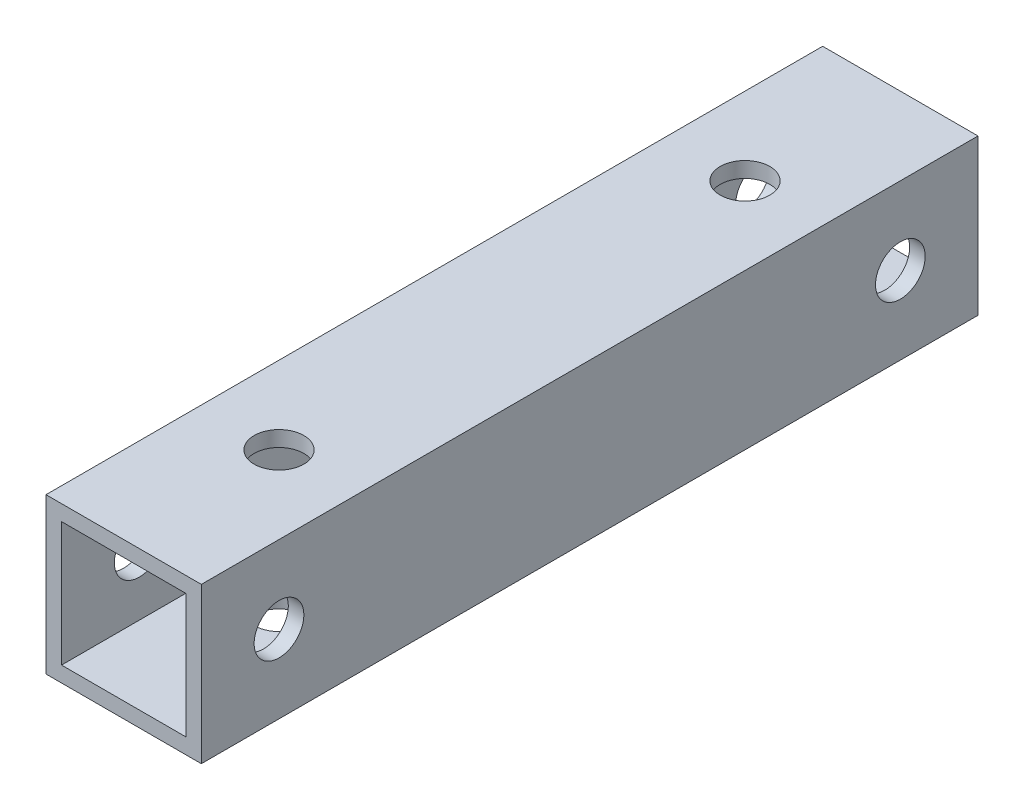
SolidWorks part; units mm, degrees
ref_plane "正面" through (0, 0, 0) normal (0, 0, 1) x (1, 0, 0)
ref_plane "平面" through (0, 0, 0) normal (0, 1, 0) x (1, 0, 0)
ref_plane "右側面" through (0, 0, 0) normal (1, 0, 0) x (0, 0, -1)
sketch "ｽｹｯﾁ1" plane through (0, 0, 0) normal (0, 0, 1) x (1, 0, 0)
  line L1 (-5, -5) -> (5, -5)
  line L2 (-5, -5) -> (-5, 5)
  line L3 (-5, 5) -> (5, 5)
  line L4 (5, -5) -> (5, 5)
  line L5 (-5, -5) -> (5, 5) construction
  line L6 (-5, 5) -> (5, -5) construction
  line L7 (-4, -4) -> (4, -4)
  line L8 (-4, -4) -> (-4, 4)
  line L9 (-4, 4) -> (4, 4)
  line L10 (4, -4) -> (4, 4)
  line L11 (-4, -4) -> (4, 4) construction
  line L12 (-4, 4) -> (4, -4) construction
  point P0 (0, 0)
  point P6 (0, 0)
  dimension "D1" = 10
  dimension "D2" = 10
  dimension "D3" = 1
extrude "ﾎﾞｽ - 押し出し1" add sketch "ｽｹｯﾁ1" along normal mid plane 50
sketch "ｽｹｯﾁ3" plane through (5, 0, 0) normal (1, 0, 0) x (0, 0, -1)
  line L0 (25, -5) -> (25, 5) construction
  line L1 (-25, -5) -> (-25, 5) construction
  circle A0 centre (-20, 0) radius 1.6
  circle A1 centre (20, 0) radius 1.6
  dimension "D1" = 3.2
  dimension "D2" = 5
  dimension "D3" = 5
extrude "ｶｯﾄ - 押し出し1" cut sketch "ｽｹｯﾁ3" against normal through all
sketch "ｽｹｯﾁ4" plane through (0, 5, 0) normal (0, 1, 0) x (1, 0, 0)
  line L0 (5, 25) -> (-5, 25) construction
  line L1 (5, -25) -> (-5, -25) construction
  circle A0 centre (0, -15) radius 1.6
  circle A1 centre (0, 15) radius 1.6
  dimension "D1" = 3.2
  dimension "D2" = 10
  dimension "D3" = 10
extrude "ｶｯﾄ - 押し出し2" cut sketch "ｽｹｯﾁ4" against normal through all
